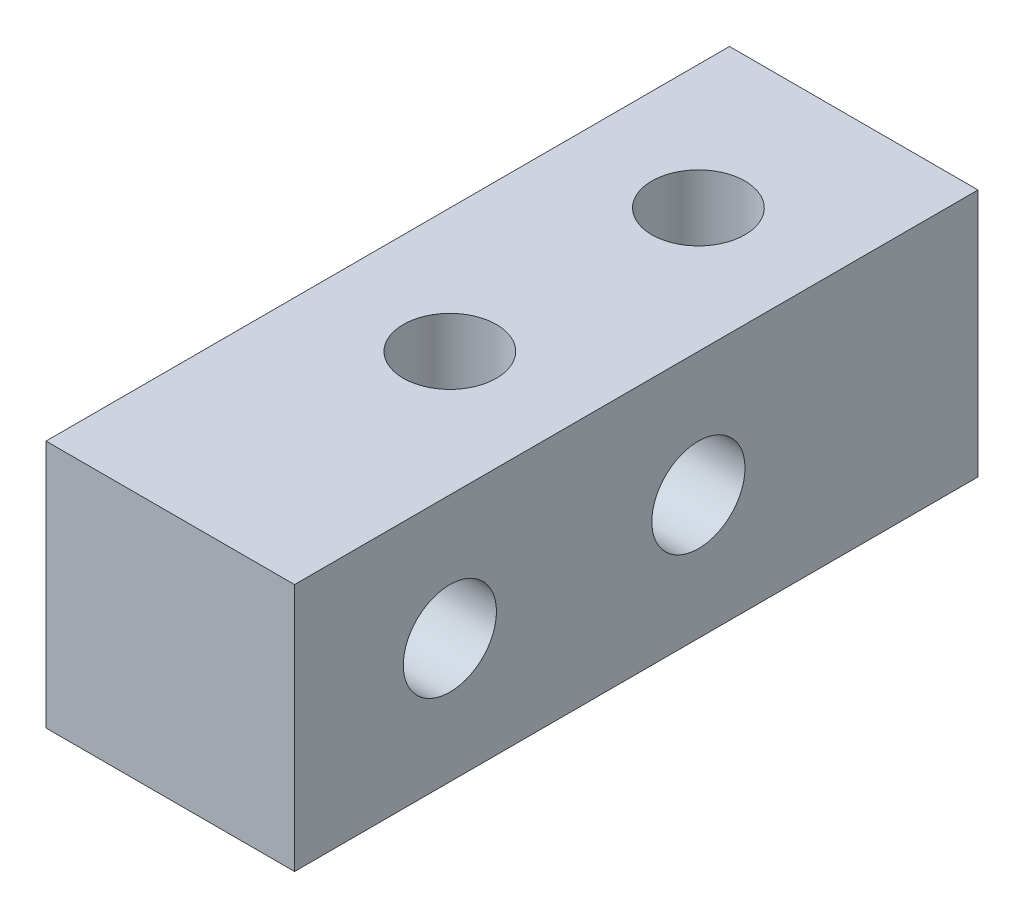
SolidWorks part; units mm, degrees
material "6061 合金"
ref_plane "前视基准面" through (0, 0, 0) normal (0, 0, 1) x (1, 0, 0)
ref_plane "上视基准面" through (0, 0, 0) normal (0, 1, 0) x (1, 0, 0)
ref_plane "右视基准面" through (0, 0, 0) normal (1, 0, 0) x (0, 0, -1)
sketch "草图1" plane through (0, 0, 0) normal (0, 0, 1) x (1, 0, 0)
  line L1 (-4, 4) -> (4, 4)
  line L2 (-4, 4) -> (-4, -4)
  line L3 (-4, -4) -> (4, -4)
  line L4 (4, 4) -> (4, -4)
  line L5 (-4, 4) -> (4, -4) construction
  line L6 (-4, -4) -> (4, 4) construction
  point P0 (0, 0)
  dimension "D1" = 8
  dimension "D2" = 8
extrude "凸台-拉伸1" add sketch "草图1" along normal blind 22
sketch "草图2" plane through (0, 4, 0) normal (0, 1, 0) x (1, 0, 0)
  line L0 (0, 0) -> (0, -22) construction
  line L1 (4, 0) -> (-4, 0) construction
  line L2 (4, -22) -> (-4, -22) construction
  circle A0 centre (0, -5) radius 1.5
  circle A1 centre (0, -13) radius 1.5
  dimension "D1" = 3
  dimension "D2" = 5
  dimension "D3" = 8
extrude "切除-拉伸1" cut sketch "草图2" against normal through all
sketch "草图3" plane through (4, 0, 0) normal (1, 0, 0) x (0, 0, -1)
  line L0 (-22, 0) -> (0, 0) construction
  line L1 (-22, -4) -> (-22, 4) construction
  circle A0 centre (-17, 0) radius 1.5
  circle A1 centre (-9, 0) radius 1.5
  dimension "D1" = 3
  dimension "D2" = 5
  dimension "D3" = 8
extrude "切除-拉伸2" cut sketch "草图3" against normal through all
